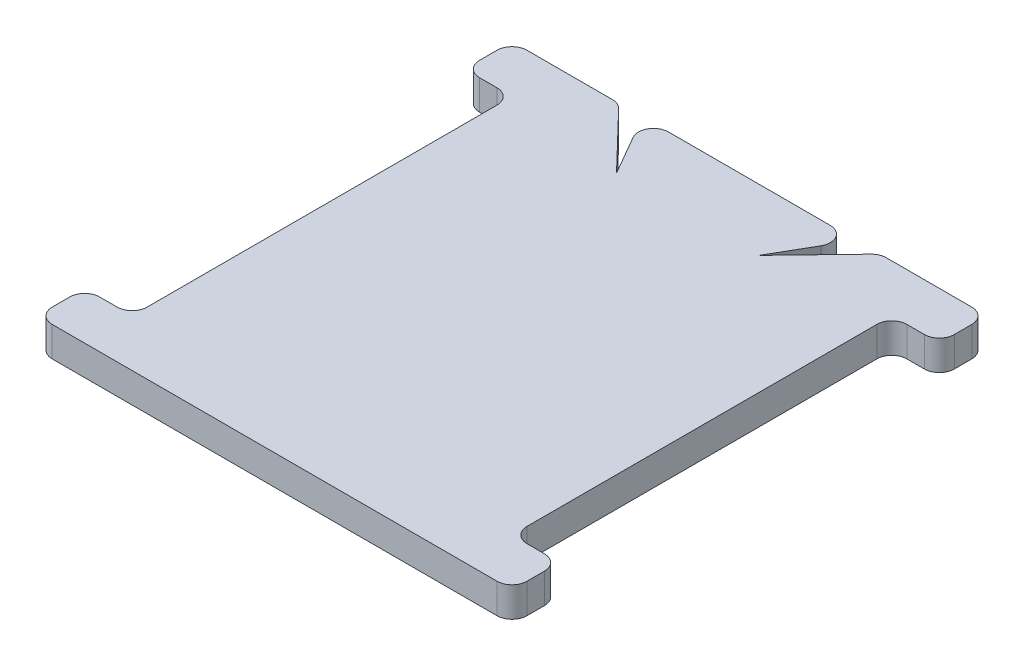
SolidWorks part; units mm, degrees
ref_plane "Front Plane" through (0, 0, 0) normal (0, 0, 1) x (1, 0, 0)
ref_plane "Top Plane" through (0, 0, 0) normal (0, 1, 0) x (1, 0, 0)
ref_plane "Right Plane" through (0, 0, 0) normal (1, 0, 0) x (0, 0, -1)
sketch "Sketch1" plane through (0, 0, 0) normal (0, 1, 0) x (1, 0, 0)
  line L0 (12.7, 12.7) -> (15.875, 12.7)
  line L2 (-12.7, -12.7) -> (-12.7, 12.7)
  line L4 (12.7, -12.7) -> (12.7, 12.7)
  line L5 (-12.7, -12.7) -> (12.7, 12.7) construction
  line L6 (-12.7, 12.7) -> (12.7, -12.7) construction
  line L7 (-15.875, 15.875) -> (15.875, 15.875)
  line L8 (-15.875, 15.875) -> (-15.875, 12.7)
  line L9 (-15.875, 12.7) -> (-12.7, 12.7)
  line L10 (15.875, 15.875) -> (15.875, 12.7)
  line L11 (-15.875, -12.7) -> (-12.7, -12.7)
  line L12 (-15.875, -12.7) -> (-15.875, -15.875)
  line L13 (-15.875, -15.875) -> (15.875, -15.875)
  line L14 (15.875, -12.7) -> (15.875, -15.875)
  line L15 (12.7, -12.7) -> (15.875, -12.7)
  point P0 (0, 0)
  point P14 (21.6307, -15.875)
  point P15 (17.8564, 12.7)
  point P16 (17.8086, -12.7)
  dimension "D1" = 25.4
  dimension "D2" = 25.4
  dimension "D3" = 3.175
  dimension "D4" = 3.175
extrude "Boss-Extrude1" add sketch "Sketch1" along normal mid plane 2
fillet "Fillet1" radius 1 12 edges at (-12.7, 0, -12.7) (12.7, 0, 12.7) (-15.875, 0, -15.875) (-15.875, 0, 12.7) (-12.7, 0, 12.7) (-15.875, 0, -12.7) (-15.875, 0, 15.875) (15.875, 0, 12.7) (15.875, 0, 15.875) (15.875, 0, -15.875) (15.875, 0, -12.7) (12.7, 0, -12.7)
sketch "Sketch2" plane through (0, 1, 0) normal (0, 1, 0) x (1, 0, 0)
  line L0 (-8.7312, 15.875) -> (-4.7625, 11.7506)
  line L1 (14.875, 15.875) -> (-14.875, 15.875) construction
  line L2 (-4.7625, 11.7506) -> (-7.1437, 15.875)
  line L3 (-8.7312, 15.875) -> (-7.1437, 15.875)
  point P4 (-4.7353, 12.5074)
  dimension "D1" = 60
  dimension "D2" = 4.7625
  dimension "D3" = 1.5875
  dimension "D4" = 4.7625
extrude "Cut-Extrude1" cut sketch "Sketch2" against normal through all both and the other way through all
fillet "Fillet2" radius 1 2 edges at (-7.1437, 0, -15.875) (-8.7312, 0, -15.875)
mirror "Mirror1" about plane through (0, 0, 0) normal (1, 0, 0) of "Fillet2", "Cut-Extrude1"
